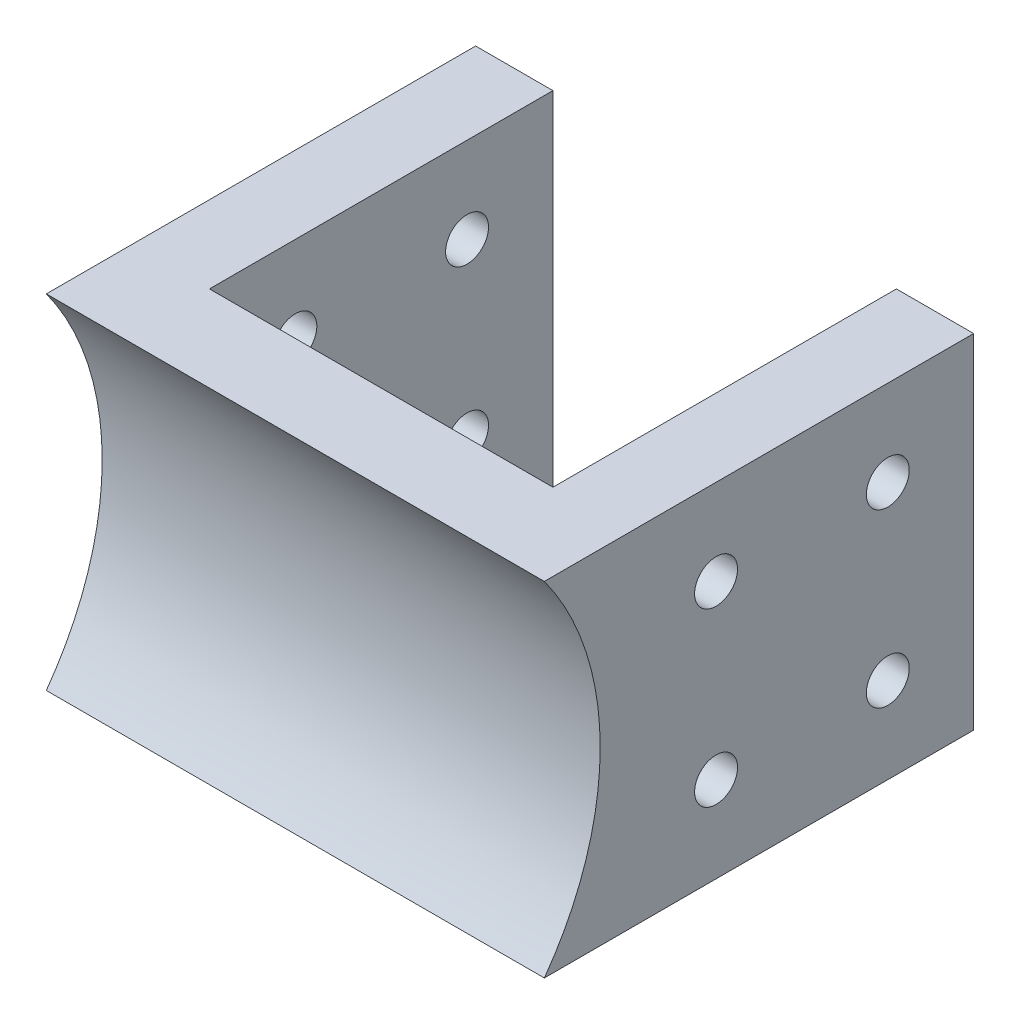
SolidWorks part; units mm, degrees
material "6061-T6 (SS)"
ref_plane "Front Plane" through (0, 0, 0) normal (0, 0, 1) x (1, 0, 0)
ref_plane "Top Plane" through (0, 0, 0) normal (0, 1, 0) x (1, 0, 0)
ref_plane "Right Plane" through (0, 0, 0) normal (1, 0, 0) x (0, 0, -1)
sketch "Sketch1" plane through (0, 0, 0) normal (0, 1, 0) x (1, 0, 0)
  line L0 (0, 0) -> (58, 0)
  line L1 (58, 0) -> (58, 50)
  line L2 (58, 50) -> (49, 50)
  line L3 (49, 50) -> (49, 10)
  line L4 (49, 10) -> (9, 10)
  line L5 (9, 10) -> (9, 50)
  line L6 (9, 50) -> (0, 50)
  line L7 (0, 50) -> (0, 0)
  dimension "D1" = 9
  dimension "D2" = 50
  dimension "D3" = 40
  dimension "D4" = 40
  dimension "D5" = 9
  dimension "D6" = 40
  dimension "D7" = 58
extrude "Boss-Extrude1" add sketch "Sketch1" along normal blind 40
sketch "Sketch4" plane through (49, 0, 0) normal (-1, 0, 0) x (0, 0, 1)
  line L0 (-30, 0) -> (-30, 5.5892)
  line L1 (-50, 0) -> (-40, 0)
  line L2 (-50, 0) -> (-50, 10)
  line L3 (-50, 10) -> (-40, 10)
  line L4 (-40, 0) -> (-40, 10)
  line L5 (-50, 0) -> (-10, 0) construction
  line L6 (-50, 20) -> (-47.3951, 20)
  line L7 (-50, 40) -> (-50, 0) construction
  circle A0 centre (-40, 10) radius 2.5
  circle A1 centre (-20, 10) radius 2.5
  circle A2 centre (-20, 30) radius 2.5
  circle A3 centre (-40, 30) radius 2.5
  dimension "D1" = 10
  dimension "D2" = 10
extrude "Cut-Extrude1" cut sketch "Sketch4" against normal through all both and the other way through all contours L4 A0 L3 | L3 A0 L4 | A1 | A3 | A2
sketch "Sketch5" plane through (58, 0, 0) normal (1, 0, 0) x (0, 0, -1)
  line L0 (0, 40) -> (0, 0)
  arc A2 (0, 0) -> (0, 40) centre (-27.4955, 20) ccw
  dimension "D3" = 68
extrude "Cut-Extrude2" cut sketch "Sketch5" against normal through all
